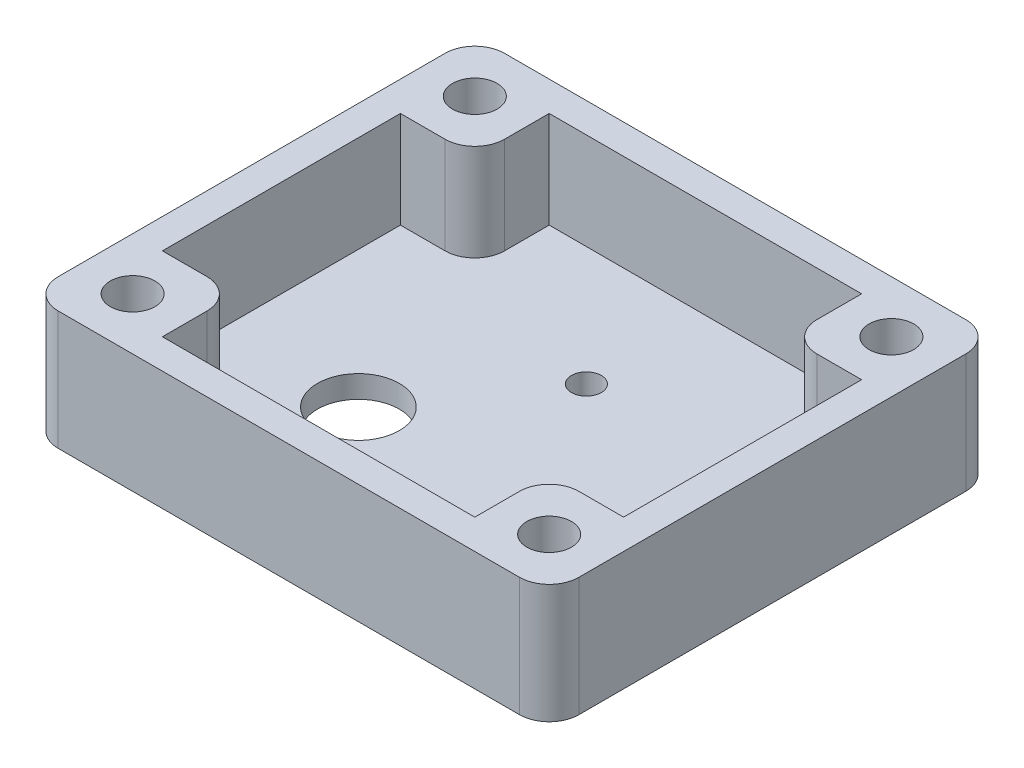
SolidWorks part; units mm, degrees
ref_plane "Front Plane" through (0, 0, 0) normal (0, 0, 1) x (1, 0, 0)
ref_plane "Top Plane" through (0, 0, 0) normal (0, 1, 0) x (1, 0, 0)
ref_plane "Right Plane" through (0, 0, 0) normal (1, 0, 0) x (0, 0, -1)
sketch "Sketch1" plane through (0, 0, 0) normal (0, 1, 0) x (1, 0, 0)
  line L0 (0, -15) -> (0, -4) construction
  line L1 (-17.5, 15) -> (17.5, 15)
  line L2 (-17.5, 15) -> (-17.5, -15)
  line L3 (-17.5, -15) -> (17.5, -15)
  line L4 (17.5, 15) -> (17.5, -15)
  line L5 (-17.5, 15) -> (17.5, -15) construction
  line L6 (-17.5, -15) -> (17.5, 15) construction
  line L7 (0, -4) -> (-6.3246, -4) construction
  line L8 (0, -4) -> (0, 5) construction
  circle A0 centre (-6.3246, -4) radius 2.75
  circle A1 centre (0, 5) radius 1
  point P0 (0, 0)
  dimension "D5" = 5.5
  dimension "D7" = 2
  dimension "D1" = 30
  dimension "D2" = 35
  dimension "D3" = 11
  dimension "D4" = 6.3246
  dimension "D6" = 9
extrude "Boss-Extrude1" add sketch "Sketch1" along normal blind 1.5
sketch "Sketch2" plane through (0, 1.5, 0) normal (0, 1, 0) x (1, 0, 0)
  line L0 (-17.5, 15) -> (-10.5, 15) construction
  line L1 (-17.5, 15) -> (17.5, 15)
  line L2 (-17.5, 15) -> (-17.5, -15)
  line L3 (-17.5, -15) -> (17.5, -15)
  line L4 (17.5, 15) -> (17.5, -15)
  line L5 (-17.5, 15) -> (17.5, -15) construction
  line L6 (-17.5, -15) -> (17.5, 15) construction
  line L7 (-10.5, 15) -> (-10.5, 13) construction
  line L8 (-10.5, 13) -> (10.5, 13)
  line L9 (10.5, 13) -> (10.5, 8)
  line L10 (10.5, 8) -> (15.5, 8)
  line L11 (15.5, 8) -> (15.5, -8)
  line L12 (15.5, -8) -> (10.5, -8)
  line L13 (10.5, -8) -> (10.5, -13)
  line L14 (10.5, -13) -> (-10.5, -13)
  line L15 (-10.5, -13) -> (-10.5, -8)
  line L16 (-10.5, -8) -> (-15.5, -8)
  line L17 (-15.5, -8) -> (-15.5, 8)
  line L18 (-15.5, 8) -> (-10.5, 8)
  line L19 (-10.5, 8) -> (-10.5, 13)
  point P0 (0, 0)
  dimension "D11" = 21
  dimension "D1" = 7
  dimension "D2" = 2
  dimension "D3" = 21
  dimension "D4" = 5
  dimension "D5" = 5
  dimension "D6" = 16
  dimension "D7" = 5
  dimension "D8" = 5
  dimension "D9" = 5
  dimension "D10" = 16
  dimension "D12" = 5
extrude "Boss-Extrude2" add sketch "Sketch2" along normal blind 6.5
sketch "Sketch3" plane through (0, 8, 0) normal (0, 1, 0) x (1, 0, 0)
  line L0 (-17.5, 15) -> (-10.5, 8) construction
  line L1 (-0.825, 0) -> (0.825, 0) construction
  line L2 (0, -0.825) -> (0, 0.825) construction
  circle A0 centre (-14, 11.5) radius 1.5
  circle A1 centre (-14, -11.5) radius 1.5
  circle A2 centre (14, -11.5) radius 1.5
  circle A3 centre (14, 11.5) radius 1.5
  dimension "D1" = 3
extrude "Cut-Extrude1" cut sketch "Sketch3" against normal through all
fillet "Fillet1" radius 2 8 edges at (-17.5, 4, -15) (10.5, 4.75, 8) (-17.5, 4, 15) (-10.5, 4.75, 8) (17.5, 4, 15) (17.5, 4, -15) (10.5, 4.75, -8) (-10.5, 4.75, -8)
